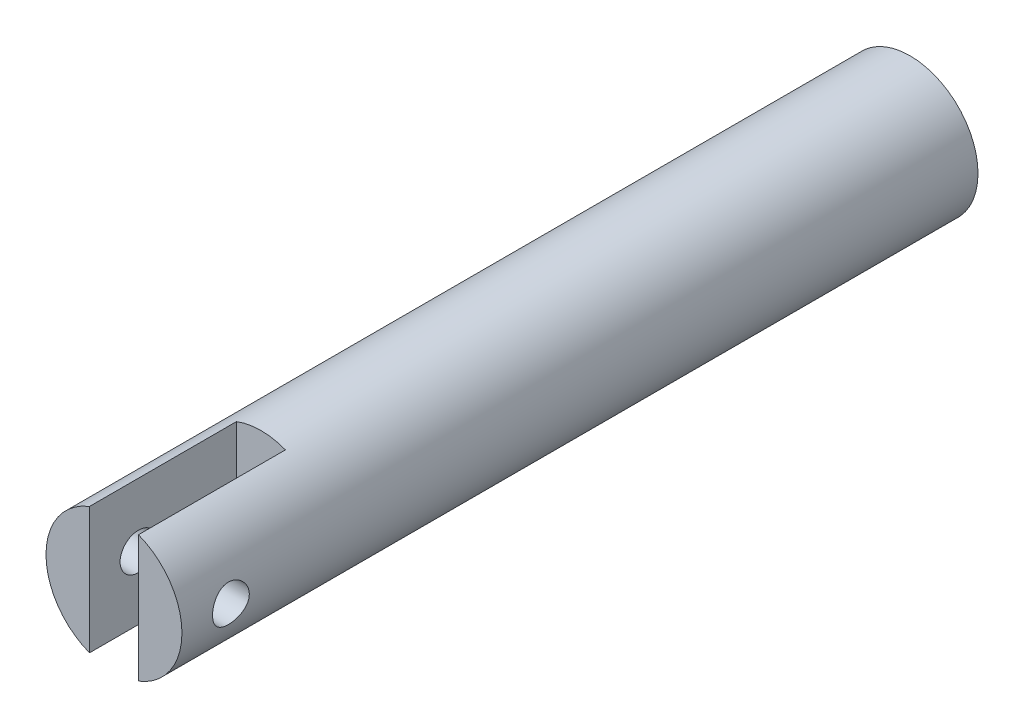
SolidWorks part; units mm, degrees
material "AISI 1020"
ref_plane "Plan de face" through (0, 0, 0) normal (0, 0, 1) x (1, 0, 0)
ref_plane "Plan de dessus" through (0, 0, 0) normal (0, 1, 0) x (1, 0, 0)
ref_plane "Plan de droite" through (0, 0, 0) normal (1, 0, 0) x (0, 0, -1)
sketch "Esquisse1" plane through (0, 0, 0) normal (0, 0, 1) x (1, 0, 0)
  circle A0 centre (0, 0) radius 5.55
  dimension "D1" = 11.1
extrude "Boss.-Extru.1" add sketch "Esquisse1" along normal blind 65
sketch "Esquisse2" plane through (0, 0, 65) normal (0, 0, 1) x (1, 0, 0)
  line L0 (0, 5.55) -> (0, -5.55) construction
  line L1 (-2, 5.1771) -> (-2, -5.1771)
  line L2 (2, 5.1771) -> (2, -5.1771)
  line L4 (-2, 5.55) -> (-2, -5.55) construction
  line L5 (2, 5.55) -> (2, -5.55) construction
  circle A0 centre (0, 0) radius 5.55 construction
  arc A1 (-2, -5.1771) -> (2, -5.1771) centre (0, 0) ccw
  arc A2 (2, 5.1771) -> (-2, 5.1771) centre (0, 0) ccw
  dimension "D1" = 2
  dimension "D2" = 2
extrude "Enlèv. mat.-Extru.1" cut sketch "Esquisse2" against normal blind 12
sketch "Esquisse3" plane through (0, 0, 0) normal (1, 0, 0) x (0, 0, -1)
  line L0 (-65, 5.1771) -> (-65, -5.1771) construction
  line L1 (-65, 0) -> (0, 0) construction
  line L2 (0, -5.55) -> (0, 5.55) construction
  circle A0 centre (-61, 0) radius 1.5
  dimension "D1" = 3
  dimension "D2" = 4
extrude "Enlèv. mat.-Extru.2" cut sketch "Esquisse3" against normal through all and the other way through all
